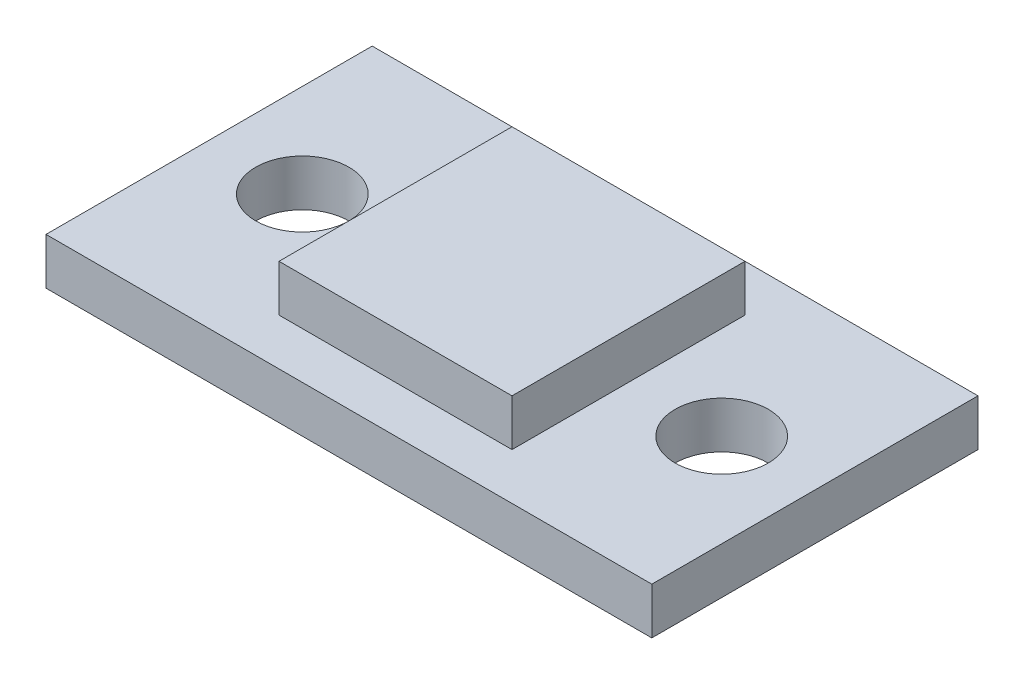
SolidWorks part; units mm, degrees
ref_plane "Plan de face" through (0, 0, 0) normal (0, 0, 1) x (1, 0, 0)
ref_plane "Plan de dessus" through (0, 0, 0) normal (0, 1, 0) x (1, 0, 0)
ref_plane "Plan de droite" through (0, 0, 0) normal (1, 0, 0) x (0, 0, -1)
sketch "Esquisse1" plane through (0, 0, 0) normal (0, 1, 0) x (1, 0, 0)
  line L1 (-2.5, 2.5) -> (2.5, 2.5)
  line L2 (-2.5, 2.5) -> (-2.5, -2.5)
  line L3 (-2.5, -2.5) -> (2.5, -2.5)
  line L4 (2.5, 2.5) -> (2.5, -2.5)
  point P4 (0, 2.5)
  point P6 (2.5, 0)
  dimension "D1" = 5
  dimension "D2" = 5
extrude "Boss.-Extru.1" add sketch "Esquisse1" along normal blind 1
sketch "Esquisse2" plane through (0, 0, 0) normal (0, -1, 0) x (1, 0, 0)
  line L0 (2.5, 2.5) -> (2.5, -2.5) construction
  line L1 (-6.5, 3.5) -> (6.5, 3.5)
  line L2 (-6.5, 3.5) -> (-6.5, -3.5)
  line L3 (-6.5, -3.5) -> (6.5, -3.5)
  line L4 (6.5, 3.5) -> (6.5, -3.5)
  line L5 (-2.5, 2.5) -> (2.5, 2.5) construction
  line L6 (0, 3.5) -> (0, -3.5) construction
  circle A0 centre (4.5, 0) radius 1
  circle A1 centre (-4.5, 0) radius 1
  point P4 (6.5, 0)
  point P7 (2.5, 0)
  point P9 (0, 3.5)
  point P13 (2.5, 0)
  dimension "D3" = 2
  dimension "D1" = 2
  dimension "D2" = 2
  dimension "D4" = 1
extrude "Boss.-Extru.2" add sketch "Esquisse2" along normal blind 1
